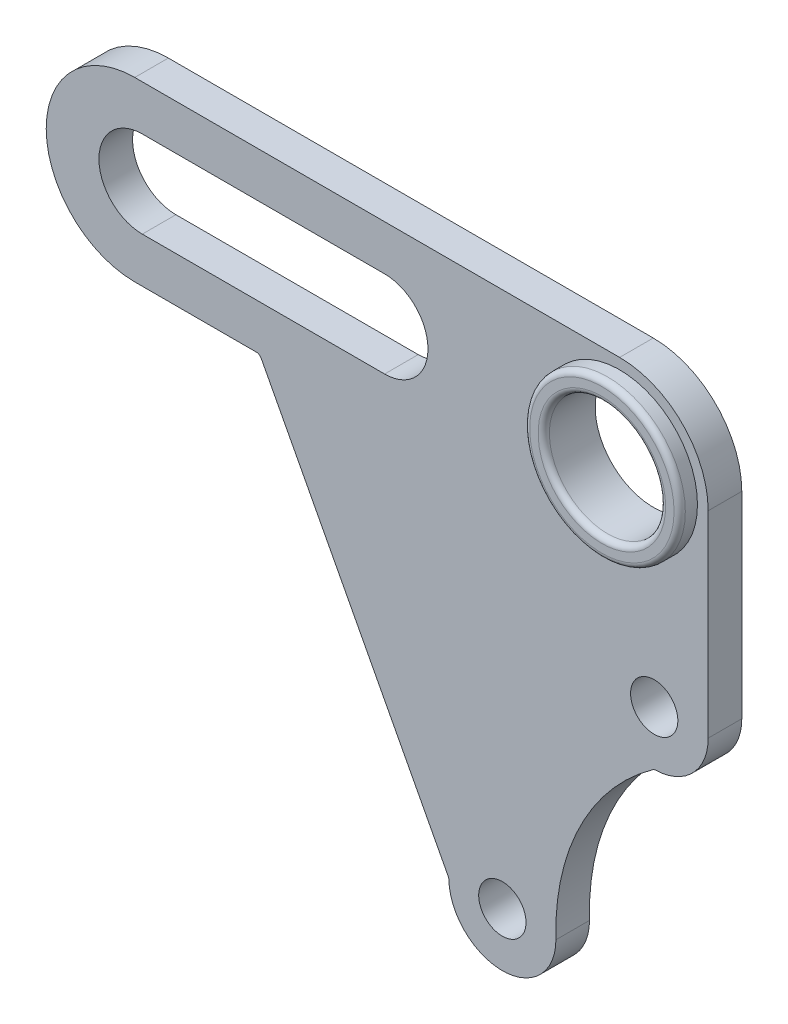
SolidWorks part; units mm, degrees
ref_plane "Front Plane" through (0, 0, 0) normal (0, 0, 1) x (1, 0, 0)
ref_plane "Top Plane" through (0, 0, 0) normal (0, 1, 0) x (1, 0, 0)
ref_plane "Right Plane" through (0, 0, 0) normal (1, 0, 0) x (0, 0, -1)
sketch "Sketch2" plane through (0, 0, 0) normal (0, 0, 1) x (1, 0, 0)
  line L0 (101.69, 15.7) -> (101.69, -73.19)
  line L1 (0, 0) -> (22.15, 0)
  line L3 (0, 31.4) -> (85.99, 31.4)
  line L4 (101.69, 0) -> (101.69, 15.7)
  line L5 (101.69, 15.7) -> (101.69, -12.4898)
  line L6 (101.69, 15.7) -> (101.69, -19.225)
  line L7 (101.69, -19.225) -> (96.3052, -19.225)
  line L8 (96.3052, -19.225) -> (92.1177, -19.225)
  line L9 (101.69, -73.19) -> (65.19, -73.19)
  line L10 (65.19, -73.19) -> (65.19, -67.89)
  line L11 (65.19, -67.89) -> (65.19, -63.695)
  line L12 (0, 0) -> (22.15, 0)
  line L13 (55.695, -63.695) -> (22.15, 0)
  line L14 (-15.7, 15.7) -> (-6.35, 15.7)
  line L18 (1.34, 23.39) -> (44.31, 23.39)
  line L19 (1.34, 8.01) -> (44.31, 8.01)
  arc A0 (0, 31.4) -> (0, 0) centre (0, 15.7) ccw
  arc A1 (101.69, 15.7) -> (85.99, 31.4) centre (85.99, 15.7) ccw
  circle A2 centre (92.1177, -19.225) radius 4.195
  arc A4 (92.1177, -28.7973) -> (101.69, -19.225) centre (92.1177, -19.225) ccw
  arc A5 (55.695, -63.695) -> (74.6736, -63.2295) centre (65.19, -63.695) ccw
  circle A6 centre (65.19, -63.695) radius 4.195
  arc A7 (74.685, -63.695) -> (92.1177, -28.7973) centre (115.8441, -62.4525) cw
  arc A8 (1.34, 23.39) -> (1.34, 8.01) centre (1.34, 15.7) ccw
  arc A9 (44.31, 8.01) -> (44.31, 23.39) centre (44.31, 15.7) ccw
  circle A10 centre (85.99, 15.7) radius 10.305
  point P4 (55.695, -63.695)
  dimension "D6" = 8.39
  dimension "D11" = 41.1779
  dimension "D12" = 7.69
  dimension "D13" = 22.15
  dimension "D17" = 20.61
  dimension "D1" = 31.4
  dimension "D2" = 9.35
  dimension "D3" = 7.69
  dimension "D4" = 34.925
  dimension "D5" = 5.3848
  dimension "D7" = 4.1875
  dimension "D8" = 36.5
  dimension "D9" = 5.3
  dimension "D10" = 4.195
  dimension "D14" = 101.69
  dimension "D15" = 117.774
  dimension "D16" = 8.01
extrude "Boss-Extrude1" add sketch "Sketch2" along normal blind 5.96
fillet "Fillet1" radius 1 3 edges at (92.1177, -28.7973, 2.98) (55.695, -63.695, 2.98) (22.15, 0, 2.98)
sketch "Sketch3" plane through (0, 0, 5.96) normal (0, 0, 1) x (1, 0, 0)
  circle A0 centre (85.99, 15.7) radius 13.8
  circle A1 centre (85.99, 15.7) radius 10.305
  dimension "D1" = 27.6
  dimension "D2" = 20.61
extrude "Boss-Extrude2" add sketch "Sketch3" along normal blind 3.15 contours A0
fillet "Fillet2" radius 1 2 edges at (96.295, 15.7, 9.11) (99.79, 15.7, 9.11)
